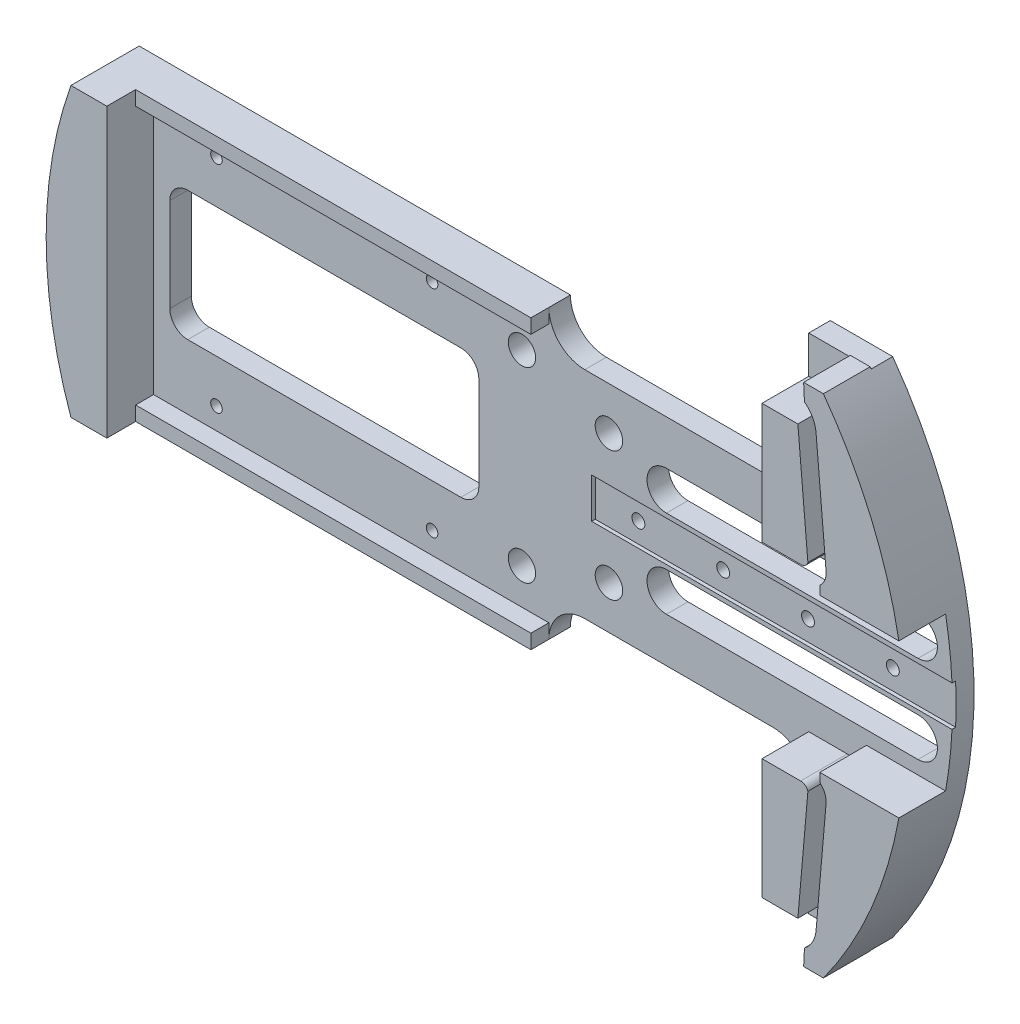
SolidWorks part; units mm, degrees
ref_plane "Front Plane" through (0, 0, 0) normal (0, 0, 1) x (1, 0, 0)
ref_plane "Top Plane" through (0, 0, 0) normal (0, 1, 0) x (1, 0, 0)
ref_plane "Right Plane" through (0, 0, 0) normal (1, 0, 0) x (0, 0, -1)
sketch "Sketch1" plane through (0, 0, 0) normal (0, 0, 1) x (1, 0, 0)
  line L0 (0, 0) -> (91.8237, 0) construction
  line L1 (10.9774, 19.05) -> (44.196, 19.05)
  line L2 (-71.5726, 25.4) -> (4.6274, 25.4)
  line L3 (10.9774, -19.05) -> (44.196, -19.05)
  line L6 (50.546, 44.45) -> (61.5792, 44.45)
  line L7 (50.546, -44.45) -> (61.5792, -44.45)
  line L11 (-71.5726, -25.4) -> (4.6274, -25.4)
  line L12 (50.546, 25.4) -> (50.546, 44.45)
  line L14 (50.546, -25.4) -> (50.546, -44.45)
  arc A0 (61.5792, -44.45) -> (61.5792, 44.45) centre (0, 0) ccw
  circle A1 centre (0, 0) radius 75.946 construction
  arc A2 (-71.5726, 25.4) -> (-71.5726, -25.4) centre (0, 0) ccw
  arc A3 (44.196, 19.05) -> (50.546, 25.4) centre (44.196, 25.4) ccw
  arc A4 (10.9774, 19.05) -> (4.6274, 25.4) centre (10.9774, 25.4) cw
  arc A5 (44.196, -19.05) -> (50.546, -25.4) centre (44.196, -25.4) cw
  arc A6 (10.9774, -19.05) -> (4.6274, -25.4) centre (10.9774, -25.4) ccw
  point P6 (75.946, 0)
  point P17 (0, 0)
  dimension "D1" = 75.946
  dimension "D8" = 151.892
  dimension "D11" = 75.946
  dimension "D2" = 76.2
  dimension "D3" = 6.35
  dimension "D4" = 25.4
  dimension "D5" = 50.8
  dimension "D6" = 88.9
  dimension "D7" = 6.35
  dimension "D9" = 6.35
  dimension "D10" = 6.35
extrude "Boss-Extrude1" add sketch "Sketch1" along normal blind 3.81
sketch "Sketch2" plane through (0, 0, 3.81) normal (0, 0, 1) x (1, 0, 0)
  line L0 (60.2463, 17.78) -> (56.2059, 64.1603) construction
  line L1 (-13.9228, 0) -> (116.9939, 0) construction
  line L2 (35.7924, 17.78) -> (109.7023, 17.78) construction
  line L3 (61.8653, 17.78) -> (60.0951, 38.1)
  line L4 (58.6516, 17.5) -> (56.8815, 37.82)
  line L5 (56.8815, 37.82) -> (50.546, 37.82)
  line L6 (58.0471, 41.7789) -> (57.9008, 44.704)
  line L7 (57.9008, 44.704) -> (61.395, 44.704)
  line L8 (50.546, 37.82) -> (50.546, 16.5667)
  line L9 (50.546, 16.5667) -> (57.3661, 16.5667)
  line L10 (60.7595, 15.0941) -> (60.7595, 13.5449)
  line L11 (60.7595, 13.5449) -> (74.7284, 13.5449)
  line L12 (60.2463, -17.78) -> (56.2059, -64.1603) construction
  line L13 (60.7595, -13.5449) -> (74.7284, -13.5449)
  line L14 (60.7595, -15.0941) -> (60.7595, -13.5449)
  line L15 (50.546, -16.5667) -> (57.3661, -16.5667)
  line L16 (50.546, -37.82) -> (50.546, -16.5667)
  line L17 (57.9008, -44.704) -> (61.395, -44.704)
  line L18 (58.0471, -41.7789) -> (57.9008, -44.704)
  line L19 (56.8815, -37.82) -> (50.546, -37.82)
  line L20 (58.6516, -17.5) -> (56.8815, -37.82)
  line L21 (61.8653, -17.78) -> (60.0951, -38.1)
  line L22 (96.3863, 0) -> (96.3863, 82.276) construction
  arc A0 (61.5792, -44.45) -> (61.5792, 44.45) centre (0, 0) ccw construction
  arc A1 (60.0951, 38.1) -> (58.0471, 41.7789) centre (54.9639, 37.653) ccw
  arc A2 (57.3661, 16.5667) -> (58.6516, 17.5) centre (57.3661, 17.9187) ccw
  arc A3 (61.8653, 17.78) -> (60.7595, 15.0941) centre (58.7167, 17.5057) cw
  arc A4 (74.7284, 13.5449) -> (61.395, 44.704) centre (0, 0) ccw
  arc A5 (74.7284, -13.5449) -> (61.395, -44.704) centre (0, 0) cw
  arc A6 (61.8653, -17.78) -> (60.7595, -15.0941) centre (58.7167, -17.5057) ccw
  arc A7 (57.3661, -16.5667) -> (58.6516, -17.5) centre (57.3661, -17.9187) cw
  arc A8 (60.0951, -38.1) -> (58.0471, -41.7789) centre (54.9639, -37.653) cw
  point P0 (75.946, 0)
  point P1 (60.2463, 17.78)
  point P49 (96.3863, 44.704)
  dimension "D6" = 75.946
  dimension "D1" = 17.78
  dimension "D2" = 15.6997
  dimension "D3" = 85.021
  dimension "D4" = 1.6129
  dimension "D5" = 20.32
  dimension "D7" = 44.704
  dimension "D8" = 44.704
  dimension "D9" = 25.4
extrude "Boss-Extrude2" add sketch "Sketch2" along normal blind 8.255
sketch "Sketch3" plane through (0, 0, 3.81) normal (0, 0, 1) x (1, 0, 0)
  line L0 (-6.3906, 0) -> (92.2963, 0) construction
  line L2 (12.192, -3.55) -> (76.962, -3.55)
  line L3 (12.192, -3.55) -> (12.192, 3.55)
  line L4 (12.192, 3.55) -> (76.962, 3.55)
  line L5 (76.962, -3.55) -> (76.962, 3.55)
  line L6 (12.192, -3.55) -> (76.962, 3.55) construction
  line L7 (12.192, 3.55) -> (76.962, -3.55) construction
  line L8 (50.546, 16.5667) -> (50.546, 25.4) construction
  point P3 (44.577, 0)
  dimension "D1" = 7.1
  dimension "D2" = 64.77
  dimension "D3" = 38.354
extrude "Cut-Extrude1" cut sketch "Sketch3" against normal blind 0.635
sketch "Sketch6" plane through (0, 0, 0) normal (0, 0, -1) x (-1, 0, 0)
  line L1 (102.4877, 0) -> (-122.8054, 0) construction
sketch "Sketch7" plane through (0, 0, 0) normal (0, 0, 1) x (1, 0, 0)
  line L0 (0, 0) -> (107.1474, 0) construction
  line L1 (0, 0) -> (65.9911, 38.1) construction
  dimension "D1" = 30
ref_plane "Plane2" through (65.7712, 37.973, 0) normal (0.866, 0.5, 0) x (0, 0, -1)
sketch "Sketch9" plane through (0, 0, 3.81) normal (0, 0, 1) x (1, 0, 0)
  line L0 (-35.0108, 0) -> (91.9546, 0) construction
  line L1 (75.863, 3.55) -> (12.192, 3.55) construction
  line L2 (69.85, 11.17) -> (25.4, 11.17)
  line L3 (69.85, 11.17) -> (69.85, 4.312) construction
  line L4 (69.85, 4.312) -> (25.4, 4.312)
  line L5 (25.4, 11.17) -> (25.4, 4.312) construction
  line L6 (69.85, -4.312) -> (25.4, -4.312)
  line L7 (69.85, -11.17) -> (25.4, -11.17)
  arc A0 (25.4, 11.17) -> (25.4, 4.312) centre (25.4, 7.741) ccw
  arc A1 (69.85, 11.17) -> (69.85, 4.312) centre (69.85, 7.741) cw
  arc A2 (69.85, -11.17) -> (69.85, -4.312) centre (69.85, -7.741) ccw
  arc A3 (25.4, -11.17) -> (25.4, -4.312) centre (25.4, -7.741) cw
  point P9 (74.93, 0)
  dimension "D1" = 6.858
  dimension "D2" = 0.762
  dimension "D3" = 44.45
  dimension "D4" = 74.93
  dimension "D5" = 5.08
extrude "Cut-Extrude4" cut sketch "Sketch9" against normal through all
sketch "Sketch10" plane through (0, 0, 3.81) normal (0, 0, 1) x (1, 0, 0)
  line L0 (50.546, 37.82) -> (50.546, 16.5667) construction
  line L1 (-5.2199, 8.255) -> (-40.7011, 8.255) construction
  line L2 (-35.052, -6.0075) -> (-35.052, 31.8531) construction
  line L3 (-10.922, 11.43) -> (-59.182, 11.43)
  line L4 (-7.747, -8.255) -> (-7.747, 8.255)
  line L5 (-82.1806, 0) -> (28.287, 0) construction
  line L6 (-62.357, -8.255) -> (-62.357, 8.255)
  line L7 (-10.922, -11.43) -> (-59.182, -11.43)
  line L8 (-102.4877, 0) -> (122.8054, 0) construction
  arc A0 (-7.747, 8.255) -> (-10.922, 11.43) centre (-10.922, 8.255) ccw
  arc A1 (-62.357, 8.255) -> (-59.182, 11.43) centre (-59.182, 8.255) cw
  arc A2 (-7.747, -8.255) -> (-10.922, -11.43) centre (-10.922, -8.255) cw
  arc A3 (-62.357, -8.255) -> (-59.182, -11.43) centre (-59.182, -8.255) ccw
  point P0 (-35.052, 0)
  point P16 (-35.052, 15.5292)
  point P19 (-4.5185, 0)
  point P22 (-35.052, 11.43)
  point P24 (-65.5855, 0)
  dimension "D1" = 16.51
  dimension "D2" = 3.175
  dimension "D3" = 48.26
  dimension "D4" = 58.293
  dimension "D5" = 3.175
  dimension "D6" = 3.175
extrude "Cut-Extrude5" cut sketch "Sketch10" against normal through all
sketch "Sketch12" plane through (0, 0, 3.81) normal (0, 0, 1) x (1, 0, 0)
  line L0 (15.24, 51.8718) -> (15.24, -46.8025) construction
  line L1 (50.546, 37.82) -> (50.546, 16.5667) construction
  line L2 (0, 0) -> (87.8985, 0) construction
  line L3 (-102.4877, 0) -> (122.8054, 0) construction
  circle A0 centre (15.24, 11.43) radius 2.4257
  circle A1 centre (15.24, -11.43) radius 2.4257
  dimension "D2" = 4.8514
  dimension "D1" = 35.306
  dimension "D3" = 11.43
extrude "Cut-Extrude6" cut sketch "Sketch12" against normal through all
sketch "Sketch4" plane through (0, 0, 3.175) normal (0, 0, 1) x (1, 0, 0)
  line L0 (12.192, 3.55) -> (12.192, -3.55) construction
  line L1 (-1.4827, 0) -> (103.4049, 0) construction
  circle A0 centre (19.812, 0) radius 1.143
  circle A1 centre (34.798, 0) radius 1.143
  circle A2 centre (49.784, 0) radius 1.143
  circle A3 centre (64.77, 0) radius 1.143
  point P2 (12.192, 0)
  dimension "D2" = 2.286
  dimension "D4" = 14.986
  dimension "D1" = 7.62
  dimension "D5" = 19.812
  dimension "D3" = 4
extrude "Cut-Extrude2" cut sketch "Sketch4" against normal blind 11.43
sketch "Sketch17" plane through (0, 0, 3.81) normal (0, 0, 1) x (1, 0, 0)
  line L0 (-87.521, 0) -> (99.4626, 0) construction
  line L1 (-102.4877, 0) -> (122.8054, 0) construction
  line L3 (-0.127, 0) -> (-0.127, 33.8266) construction
  line L5 (-7.747, -8.255) -> (-7.747, 8.255) construction
  circle A0 centre (-0.127, 16.51) radius 2.413
  circle A2 centre (-0.127, -16.51) radius 2.413
  dimension "D1" = 4.826
  dimension "D2" = 16.51
  dimension "D3" = 7.62
extrude "Cut-Extrude9" cut sketch "Sketch17" against normal through all
sketch "Sketch19" plane through (0, 0, 3.81) normal (0, 0, 1) x (1, 0, 0)
  line L0 (-71.5726, -25.4) -> (4.6274, -25.4) construction
  line L3 (-71.5726, -25.4) -> (-65.2226, -25.4)
  line L4 (-65.2226, -25.4) -> (-65.2226, 25.4)
  line L5 (4.6274, 25.4) -> (-71.5726, 25.4) construction
  line L6 (-65.2226, 25.4) -> (-71.5726, 25.4)
  circle A0 centre (0, 0) radius 75.946 construction
  arc A3 (-71.5726, 25.4) -> (-71.5726, -25.4) centre (0, 0) ccw
  point P0 (-65.2226, -25.4)
  point P6 (-71.5726, -25.4)
  dimension "D2" = 151.892
  dimension "D1" = 6.35
extrude "Boss-Extrude5" add sketch "Sketch19" along normal blind 8.255
sketch "Sketch20" plane through (0, -25.4, 0) normal (0, -1, 0) x (1, 0, 0)
  line L0 (-65.2226, 3.81) -> (4.6274, 3.81)
  line L1 (4.6274, 3.81) -> (4.6274, 6.985)
  line L2 (4.6274, 6.985) -> (-65.2226, 6.985)
  line L3 (-65.2226, 12.065) -> (-65.2226, 3.81) construction
  line L4 (-65.2226, 6.985) -> (-65.2226, 3.81)
  dimension "D1" = 3.175
extrude "Boss-Extrude6" add sketch "Sketch20" against normal blind 2.54
mirror "Mirror1" about plane through (0, 0, 0) normal (0, 1, 0) of "Boss-Extrude6"
sketch "Sketch21" plane through (0, 0, 0) normal (0, 0, -1) x (-1, 0, 0)
  line L1 (16.002, -19.05) -> (54.102, -19.05) construction
  line L2 (16.002, -19.05) -> (16.002, 19.05) construction
  line L3 (16.002, 19.05) -> (54.102, 19.05) construction
  line L4 (54.102, -19.05) -> (54.102, 19.05) construction
  line L5 (16.002, -19.05) -> (54.102, 19.05) construction
  line L6 (16.002, 19.05) -> (54.102, -19.05) construction
  line L12 (35.052, 11.43) -> (35.052, -11.43) construction
  line L13 (10.922, 11.43) -> (59.182, 11.43) construction
  line L14 (59.182, -11.43) -> (10.922, -11.43) construction
  circle A0 centre (54.102, 19.05) radius 1.0224
  circle A1 centre (16.002, 19.05) radius 1.0223
  circle A2 centre (16.002, -19.05) radius 1.0223
  circle A3 centre (54.102, -19.05) radius 1.0224
  point P14 (35.052, 0)
  point P15 (35.052, 0)
  point P16 (35.052, 0)
  dimension "D3" = 2.0447
  dimension "D5" = 2.0447
  dimension "D6" = 2.0447
  dimension "D7" = 2.0447
  dimension "D1" = 38.1
  dimension "D2" = 38.1
extrude "Cut-Extrude10" cut sketch "Sketch21" against normal through all
equation "\"0.15inin\"=0.2"
equation "\"0.45inin\"=0.35"
equation "\"0.55inin\"=0.45"
equation "\"0.125inin\"=0.325"
